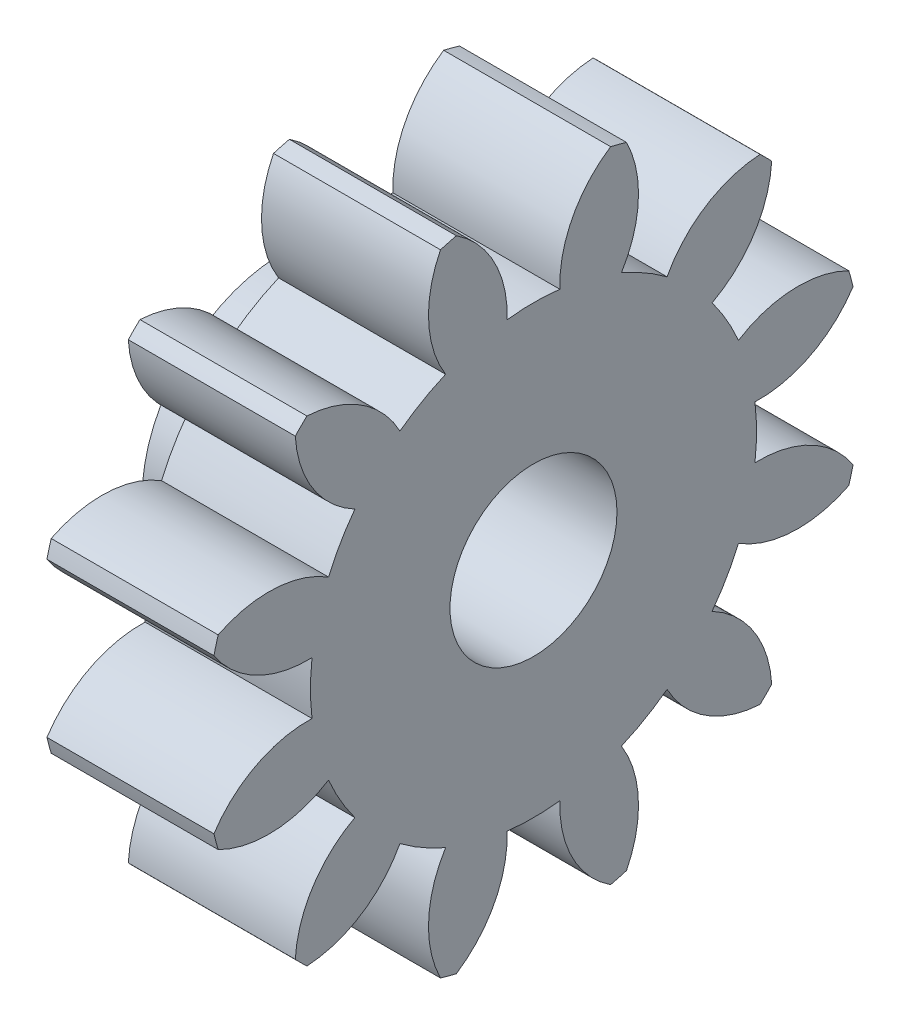
SolidWorks part; units mm, degrees
material "PLA"
ref_plane "Plane1" through (0, 0, 0) normal (0, 0, 1) x (1, 0, 0)
ref_plane "Plane2" through (0, 0, 0) normal (0, 1, 0) x (1, 0, 0)
ref_plane "Plane3" through (0, 0, 0) normal (1, 0, 0) x (0, 0, -1)
other "Configuration Table"
sketch "HoldingSke" plane through (0, 0, 0) normal (0, 1, 0) x (1, 0, 0)
  line L0 (0, 0) -> (0.8695, -0.1848)
  line L1 (-15, 0) -> (100, 0) construction
  line L2 (0, 0) -> (-2.1039, 2.3779)
  line L3 (0, 0) -> (-11.863, 4.5341)
  line L4 (0, 0) -> (8.4473, 1.7955)
  line L5 (0, 0) -> (-46.8476, -17.4728)
  line L6 (0, 0) -> (-3.3159, -2.2372)
  line L7 (-2.1039, 2.3779) -> (8.6586, 51.2059)
  line L8 (-76.2, 54.61) -> (-75.7, 54.61)
  line L9 (-71.009, 38.7566) -> (-53.1078, 45.2721)
  line L10 (-76.2, 71.12) -> (104.1128, 71.12)
  line L11 (0, 0) -> (-4, 0)
  line L12 (-76.2, 101.6) -> (-76.158, 101.6)
  line L13 (24.9733, 27.94) -> (52.9518, 28.4284)
  line L14 (24.9733, 27.94) -> (24.9743, 27.94)
  line L15 (24.9733, 27.94) -> (100.4006, 29.5858)
  line L16 (-63.627, -1.125) -> (-12.827, -1.125)
  circle A0 centre (0, 0) radius 1.5
  circle A1 centre (0, 0) radius 5.3427
  circle A2 centre (0, 0) radius 37.5
  circle A3 centre (0, 0) radius 1.5
  dimension "MHD" = 10.6855
  dimension "Hub_dia" = 75
  dimension "Bore" = 3
  dimension "MBD" = 3
  dimension "Num_teeth" = 12
  dimension "Pitch" = 0.8889
  dimension "Overall_len" = 50
  dimension "Show_teeth" = 12
  dimension "Thickness" = 4
  dimension "OAL" = 50.0001
  dimension "T_dim" = 0.5
  dimension "Ap" = 20
  dimension "H" = 19.05
  dimension "Pitch_radius" = 180.3128
  dimension "Width" = 4
  dimension "Backlash" = 0.042
  dimension "Addendum_fac" = 1
  dimension "Dedendum_fac" = 1.25
  dimension "Clearance_fac" = 0.25
  dimension "Dedendum_add" = 0.001
  dimension "Module" = 1.125
sketch "BasProSke" plane through (0, 0, 0) normal (0, 1, 0) x (1, 0, 0)
  line L0 (-10, 0) -> (60, 0) construction
  line L1 (0, 0) -> (0, 7.875)
  line L2 (0, 0) -> (4, 0)
  line L3 (4, 0) -> (4, 7.875)
  line L4 (4, 7.875) -> (0, 7.875)
  dimension "Thickness" = 4
  dimension "Diameter" = 15.75
revolve "Base-Revolve" add sketch "BasProSke" angle 360 about L0
sketch "TooCutSke" plane through (0, 0, 0) normal (1, 0, 0) x (0, 0, -1)
  line L1 (0, 0) -> (0, 107) construction
  line L2 (0, 0) -> (-0.9544, 6.6822) construction
  line L3 (0, 0) -> (-3.469, 12.9463) construction
  line L4 (-0.9544, 6.6822) -> (-1.7345, 6.4732) construction
  arc A0 (0.6314, 5.3053) -> (-0.6314, 5.3053) centre (0, 0) ccw
  arc A1 (1.8767, 7.6743) -> (-1.8767, 7.6743) centre (0, 0) ccw
  circle A2 centre (0, 0) radius 6.75 construction
  circle A3 centre (0, 0) radius 6.3429 construction
  arc A4 (-0.6314, 5.3053) -> (-1.8767, 7.6743) centre (-3.3298, 5.3986) ccw
  arc A5 (1.8767, 7.6743) -> (0.6314, 5.3053) centre (3.3298, 5.3986) ccw
  dimension "Root_dia" = 10.6855
  dimension "Overcut_dia" = 15.8008
  dimension "Pitch_dia" = 13.5
  dimension "Base_dia" = 12.6859
  dimension "Flank_rad" = 2.7
  dimension "Half_ang" = 15
  dimension "Half_CT" = 0.8076
extrude "ToothCut" cut sketch "TooCutSke" along normal through all
fillet "Breaks" [suppressed] radius 0.0225
fillet "RootFillets" [suppressed] radius 0.2823
pattern_circular "TeethCuts" count 12 every 30 about axis through (-10, 0, 0) along (1, 0, 0) of "ToothCut", "RootFillets", "Breaks"
sketch "HubNeaOneSke" plane through (0, 0, 0) normal (-1, 0, 0) x (0, 0, 1)
  circle A0 centre (0, 0) radius 5.3427
  dimension "Diameter" = 10.6855
extrude "HubNearOne" [suppressed] add sketch "HubNeaOneSke" along normal blind 46.0001
sketch "HubNeaBotSke" plane through (0, 0, 0) normal (-1, 0, 0) x (0, 0, 1)
  circle A0 centre (0, 0) radius 5.3427
  dimension "Diameter" = 10.6855
extrude "HubNearBoth" [suppressed] add sketch "HubNeaBotSke" along normal blind 23
ref_plane "FarPln" through (4, 0, 0) normal (1, 0, 0) x (0, 0, -1)
sketch "HubFarSke" plane through (4, 0, 0) normal (1, 0, 0) x (0, 0, -1)
  circle A0 centre (0, 0) radius 5.3427
  dimension "Diameter" = 10.6855
extrude "HubFar" [suppressed] add sketch "HubFarSke" along normal blind 23
sketch "BorSke" plane through (0, 0, 0) normal (1, 0, 0) x (0, 0, -1)
  circle A0 centre (0, 0) radius 1
  dimension "Diameter" = 2
extrude "Bore" cut sketch "BorSke" along normal mid plane 100.0001
sketch "KeySke" plane through (0, 0, 0) normal (1, 0, 0) x (0, 0, -1)
  line L0 (-0.6, 0) -> (-0.6, 2)
  line L1 (-0.6, 2) -> (0.6, 2)
  line L2 (0.6, 2) -> (0.6, 0)
  line L3 (0, 0) -> (0, 34) construction
  line L4 (-0.6, 0) -> (0.6, 0)
  dimension "Offset" = 2
  dimension "Width" = 1.2
extrude "Keyway" [suppressed] cut sketch "KeySke" along normal mid plane 100.0001
pattern_circular "Keyway2" [suppressed] count 2 every 90 about axis through (-10, 0, 0) along (1, 0, 0)
sketch "Sketch1" plane through (0, 0, 0) normal (-1, 0, 0) x (0, 0, 1)
  circle A0 centre (0, 0) radius 2.375
  circle A1 centre (0, 0) radius 3.375
  dimension "D1" = 4.75
  dimension "D2" = 1
extrude "Boss-Extrude1" add sketch "Sketch1" along normal blind 2
sketch "Sketch2" plane through (4, 0, 0) normal (1, 0, 0) x (0, 0, -1)
  circle A0 centre (0, 0) radius 2
  dimension "D1" = 4
extrude "Cut-Extrude1" cut sketch "Sketch2" against normal offset from surface (3 mm away) 3 up to face at (-2, 0, 3.375)
equation "' \"Module@HoldingSke\" = 6.35"
equation "' \"Num_teeth@HoldingSke\" = 12"
equation "' \"Ap@HoldingSke\" =  20"
equation "' \"Ap@HoldingSke\" = 20"
equation "' \"Width@HoldingSke\" = 0.5 * 25.4"
equation "' \"Hub_dia@HoldingSke\"= 1 * 25.4"
equation "' \"Hub_dia@HoldingSke\" = 1 * 25.4"
equation "' \"Overall_len@HoldingSke\" = 1.0 * 25.4"
equation "' \"Bore@HoldingSke\" = 0.75 * 25.4"
equation "' \"T_dim@HoldingSke\" = 0.1 * 25.4"
equation "' \"Width@KeySke\" = 0.25 * 25.4"
equation "' \"Show_teeth@HoldingSke\" = 13"
equation "' \"Backlash@HoldingSke\" = 0.009 * 25.4"
equation "' \"Addendum_fac@HoldingSke\" = 1.0"
equation "' \"Dedendum_fac@HoldingSke\" = 1.25"
equation "' \"Dedendum_add@HoldingSke\" = 0.00005 * 25.4"
equation "' \"Clearance_fac@HoldingSke\" = 0.25"
equation "\"Pitch@HoldingSke\" = 1 / \"Module@HoldingSke\""
equation "\"Overcut_dia@TooCutSke\" = (\"Num_teeth@HoldingSke\" + 2 * \"Addendum_fac@HoldingSke\") / \"Pitch@HoldingSke\" + 0.002 * 25.4"
equation "\"Pitch_dia@TooCutSke\" = \"Num_teeth@HoldingSke\" / \"Pitch@HoldingSke\""
equation "\"Base_dia@TooCutSke\" = \"Num_teeth@HoldingSke\" / \"Pitch@HoldingSke\" * cos((\"Ap@HoldingSke\"  * 3.14159265 / 180))"
equation "\"Root_dia@TooCutSke\" = (\"Num_teeth@HoldingSke\" + 2) / \"Pitch@HoldingSke\" - 2 * (\"Addendum_fac@HoldingSke\" + \"Dedendum_fac@HoldingSke\") / \"Pitch@HoldingSke\" - \"Dedendum_add@HoldingSke\" * 2"
equation "\"Half_ang@TooCutSke\" = 180 / \"Num_teeth@HoldingSke\""
equation "\"Half_CT@TooCutSke\" = \"Num_teeth@HoldingSke\" / \"Pitch@HoldingSke\" * sin((3.14159265 / 2 / \"Num_teeth@HoldingSke\")) / 2 - 7 * \"Backlash@HoldingSke\" / 4"
equation "\"Flank_rad@TooCutSke\" = \"Num_teeth@HoldingSke\" / \"Pitch@HoldingSke\" / 5"
equation "\"Radius@RootFillets\" = \"Clearance_fac@HoldingSke\" / \"Pitch@HoldingSke\" + \"Dedendum_add@HoldingSke\""
equation "\"Break_rad@Breaks\" = 0.02 / \"Pitch@HoldingSke\""
equation "\"Thickness@HoldingSke\" = \"Width@HoldingSke\""
equation "\"OAL@HoldingSke\" = \"Thickness@HoldingSke\""
equation "\"MHD@HoldingSke\" = (\"Num_teeth@HoldingSke\" + 2) / \"Pitch@HoldingSke\" - 2 * (\"Addendum_fac@HoldingSke\" + \"Dedendum_fac@HoldingSke\")  / \"Pitch@HoldingSke\" - \"Dedendum_add@HoldingSke\" * 2"
equation "\"MBD@HoldingSke\" = (\"Num_teeth@HoldingSke\" + 2) / \"Pitch@HoldingSke\" - 2 * (\"Addendum_fac@HoldingSke\" + \"Dedendum_fac@HoldingSke\")  / \"Pitch@HoldingSke\" - \"Dedendum_add@HoldingSke\" * 2 - 0.002 * 25.4"
equation "\"MHD@HoldingSke\" = ((sgn( \"MHD@HoldingSke\" - \"Hub_dia@HoldingSke\" )-1)*( \"MHD@HoldingSke\" - \"Hub_dia@HoldingSke\" ))/-2+ \"Hub_dia@HoldingSke\""
equation "\"MBD@HoldingSke\" = ((sgn( \"MBD@HoldingSke\" - \"Bore@HoldingSke\" )-1)*( \"MBD@HoldingSke\" - \"Bore@HoldingSke\" ))/-2+ \"Bore@HoldingSke\""
equation "\"OAL@HoldingSke\" = ((sgn( \"OAL@HoldingSke\" - \"Overall_len@HoldingSke\" )+1)*( \"OAL@HoldingSke\" - \"Overall_len@HoldingSke\" ))/2 + \"Overall_len@HoldingSke\" + 0.000002 * 25.4"
equation "\"Num_teeth@TeethCuts\" = int( \"Show_teeth@HoldingSke\" ) + 1"
equation "\"Num_teeth@TeethCuts\" = ((sgn( \"Num_teeth@TeethCuts\" - \"Num_teeth@HoldingSke\" )-1)*( \"Num_teeth@TeethCuts\" - \"Num_teeth@HoldingSke\" ))/-2+ \"Num_teeth@HoldingSke\""
equation "\"Num_teeth@TeethCuts\" = ((sgn( \"Num_teeth@TeethCuts\" - 2.0)+1)*( \"Num_teeth@TeethCuts\" - 2.0))/2 +2.0"
equation "\"Angle@TeethCuts\" = 360.0 / \"Num_teeth@HoldingSke\""
equation "\"Diameter@BasProSke\" = (\"Num_teeth@HoldingSke\" + 2 * \"Addendum_fac@HoldingSke\") / \"Pitch@HoldingSke\""
equation "\"Thickness@BasProSke\"  = \"Thickness@HoldingSke\""
equation "' \"Fillet_rad@BasProSke\" =  \"Thickness@HoldingSke\" * 0.05"
equation "' \"Fillet_rad@BasProSke\" = \"Thickness@HoldingSke\" * 0.05"
equation "\"MHD@HoldingSke\" = ((sgn( \"MHD@HoldingSke\" - \"Root_dia@TooCutSke\" )-1)*( \"MHD@HoldingSke\" - \"Root_dia@TooCutSke\" ))/-2+ \"Root_dia@TooCutSke\""
equation "\"Diameter@HubNeaOneSke\" = \"MHD@HoldingSke\""
equation "\"Length@HubNearOne\" = \"OAL@HoldingSke\" - \"Thickness@BasProSke\""
equation "\"Diameter@HubNeaBotSke\" = \"MHD@HoldingSke\""
equation "\"Length@HubNearBoth\" = ( \"OAL@HoldingSke\" - \"Thickness@BasProSke\" ) / 2.0"
equation "\"Thickness@FarPln\" = \"Thickness@BasProSke\""
equation "\"Diameter@HubFarSke\" = \"MHD@HoldingSke\""
equation "\"Length@HubFar\" = ( \"OAL@HoldingSke\" - \"Thickness@BasProSke\" ) / 2.0"
equation "\"D1@Bore\" = \"OAL@HoldingSke\" * 2.0"
equation "\"D1@Keyway\" = \"OAL@HoldingSke\" * 2.0"
equation "\"Offset@KeySke\" = \"T_dim@HoldingSke\" + \"MBD@HoldingSke\" / 2.0"
